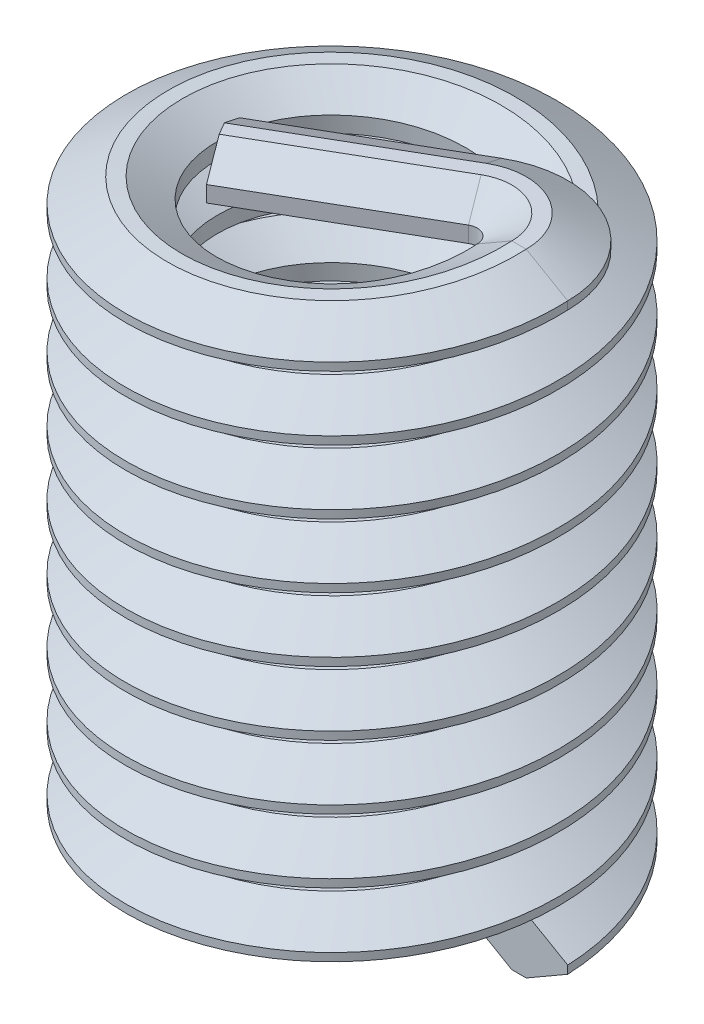
SolidWorks part; units mm, degrees
material "18-8 Stainless Steel"
ref_plane "Front Plane" through (0, 0, 0) normal (0, 0, 1) x (1, 0, 0)
ref_plane "Top Plane" through (0, 0, 0) normal (0, 1, 0) x (1, 0, 0)
ref_plane "Right Plane" through (0, 0, 0) normal (1, 0, 0) x (0, 0, -1)
sketch "Sketch1" plane through (0, 0, 0) normal (0, 0, 1) x (-1, 0, 0)
  line L0 (0, 0) -> (0, 9.525) construction
  line L1 (-0.6969, 0) -> (-1.0433, 0.2) construction
  line L2 (-1.0469, 0.2) -> (-1.3933, 0) construction
  line L3 (-1.3933, 0) -> (-1.0469, -0.2) construction
  line L4 (-1.0433, -0.2) -> (-0.6969, 0) construction
  line L5 (-1.0433, -0.2) -> (-1.0433, 0.2) construction
  line L6 (-0.6969, 0) -> (0, 0) construction
  line L8 (-1.35, -0.025) -> (-1.0902, -0.175)
  line L9 (-1, -0.175) -> (-0.7835, -0.05)
  line L10 (-0.7402, -0.025) -> (-0.7402, 0.025) construction
  line L11 (-0.7835, 0.05) -> (-1, 0.175)
  line L12 (-1.0902, 0.175) -> (-1.35, 0.025)
  line L13 (-0.6969, 0) -> (-0.7402, 0) construction
  line L14 (-0.7402, 0) -> (-1, 0) construction
  line L15 (-1.0902, 0) -> (-1.35, 0) construction
  line L16 (-1.35, 0) -> (-1.3933, 0) construction
  line L17 (-1.0902, 0.175) -> (-1, 0.175)
  line L18 (-1, 0.175) -> (-1, -0.175) construction
  line L19 (-1, -0.175) -> (-1.0902, -0.175)
  line L20 (-1.0902, -0.175) -> (-1.0902, 0.175) construction
  line L21 (-1.0902, 0) -> (-1.0433, 0) construction
  line L22 (-1.0433, 0) -> (-1, 0) construction
  line L23 (-1.35, 0.2) -> (-1.35, -3.8) construction
  line L24 (-0.7835, -0.05) -> (-0.7835, 0.05)
  line L25 (-0.7835, 0) -> (-0.7402, 0) construction
  line L26 (-1.35, -0.025) -> (-1.35, 0.025)
  line L28 (1.35, 0.2) -> (1.35, -3.8) construction
  line L29 (-1.0433, -0.2) -> (-1.0469, -0.2) construction
  line L31 (-1.0469, 0.2) -> (-1.0433, 0.2) construction
sketch "Sketch2" plane through (0, 0, 0) normal (0, 1, 0) x (1, 0, 0)
  circle A0 centre (0, 0) radius 1
curve "Helix/Spiral1" pitch 0.4 height 3.6 turns 9 parameters "Height"=3.6, "Pitch"=0.4
sweep "Sweep1" add profiles "Sketch1" path "Helix/Spiral1"
sketch "Sketch3" plane through (0, 0, 0) normal (0, 0, -1) x (-1, 0, 0)
  line L0 (-5.4053, 0.8816) -> (-0.6969, 3.6) construction
  line L1 (-8.3368, 8.0109) -> (-0.6969, 3.6) construction
  line L2 (-0.6969, 3.6) -> (-0.6969, 3.7) construction
  line L8 (-1, 3.425) -> (-0.7835, 3.55)
  line L9 (-0.7835, 3.55) -> (-0.7835, 3.65)
  line L10 (-0.7835, 3.65) -> (-1, 3.775)
  line L12 (-1.0902, 3.775) -> (-1.35, 3.625)
  line L13 (-1.35, 3.625) -> (-1.35, 3.575)
  line L14 (-1.35, 3.575) -> (-1.0902, 3.425)
  line L16 (-1, 3.425) -> (-0.7835, 3.55)
  line L17 (-0.7835, 3.55) -> (-0.7835, 3.65)
  line L18 (-0.7835, 3.65) -> (-1, 3.775)
  line L20 (-1.0902, 3.775) -> (-1.35, 3.625)
  line L21 (-1.35, 3.625) -> (-1.35, 3.575)
  line L22 (-1.35, 3.575) -> (-1.0902, 3.425)
  line L23 (-1, 3.775) -> (-1.0902, 3.775)
  line L24 (-1, 3.775) -> (-1.0902, 3.775)
  line L25 (-1.0902, 3.425) -> (-1, 3.425)
  line L26 (-1.0902, 3.425) -> (-1, 3.425)
  dimension "D1" = 0
revolve "Revolve1" add sketch "Sketch3" angle 120 about L2
sketch "Sketch4" plane through (0.5227, 0, -0.3018) normal (-0.866, 0, 0.5) x (0.5, 0, 0.866)
  line L8 (-0.0449, 3.425) -> (0.0453, 3.425)
  line L9 (0.0453, 3.425) -> (0.2618, 3.55)
  line L10 (0.2618, 3.55) -> (0.2618, 3.65)
  line L11 (0.2618, 3.65) -> (0.0453, 3.775)
  line L12 (-0.0449, 3.425) -> (0.0453, 3.425)
  line L13 (-0.0449, 3.775) -> (-0.3047, 3.625)
  line L14 (-0.3047, 3.625) -> (-0.3047, 3.575)
  line L15 (-0.3047, 3.575) -> (-0.0449, 3.425)
  line L17 (0.0453, 3.425) -> (0.2618, 3.55)
  line L18 (0.2618, 3.55) -> (0.2618, 3.65)
  line L19 (0.2618, 3.65) -> (0.0453, 3.775)
  line L21 (-0.0449, 3.775) -> (-0.3047, 3.625)
  line L22 (-0.3047, 3.625) -> (-0.3047, 3.575)
  line L23 (-0.3047, 3.575) -> (-0.0449, 3.425)
  spline S4 degree 1 poles (3000.0295, 3.775) (-3000.0216, 3.775) knots -33262.057828 -33262.057828 33262.976537 33262.976537 only from (0.0453, 3.775) to (-0.0449, 3.775)
  spline S5 degree 1 poles (0.0453, 3.775) (-0.0449, 3.775) knots 0 0 1 1
  dimension "D1" = 0
extrude "Extrude1" add sketch "Sketch4" along normal blind 1.2
equation "\"D3@Sketch1\" = \"Pitch@Helix/Spiral1\""
equation "\"D4@Sketch1\" = \"D3@Sketch1\"  * 1 / 8"
equation "\"D1@Extrude1\" = \"Thread Size@Sketch1\" * 0.6"
equation "\"Height@Helix/Spiral1\" = \"Installed Length@Sketch1\" - \"Pitch@Helix/Spiral1\""
